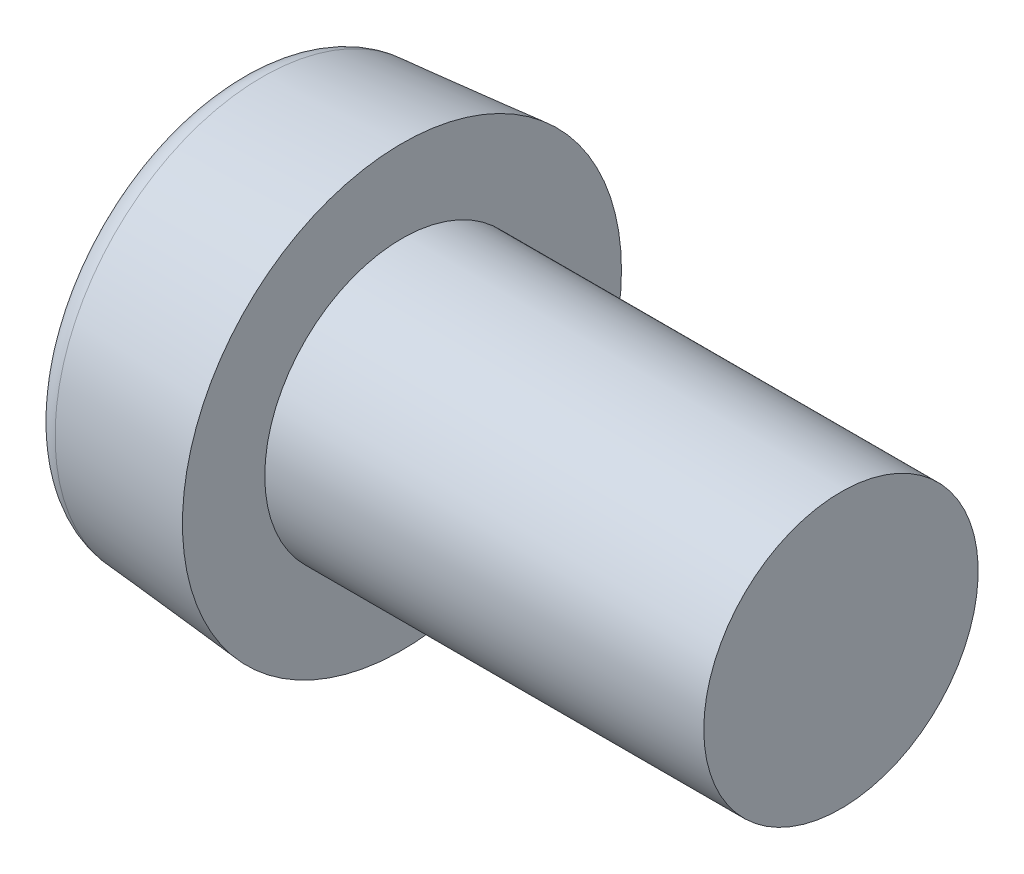
SolidWorks part; units mm, degrees
ref_plane "Front" through (0, 0, 0) normal (0, 0, 1) x (1, 0, 0)
ref_plane "Top" through (0, 0, 0) normal (0, 1, 0) x (1, 0, 0)
ref_plane "Right" through (0, 0, 0) normal (1, 0, 0) x (0, 0, -1)
ref_plane "Plane1" through (6, 0, 0) normal (1, 0, 0) x (0, 0, -1)
sketch "Sketch1" plane through (6, 0, 0) normal (1, 0, 0) x (0, 0, -1)
  circle A0 centre (0, 0) radius 8
  dimension "dk" = 16
extrude "BaseHead" add sketch "Sketch1" against normal blind 6 draft 5
sketch "Sketch2" plane through (6, 0, 0) normal (1, 0, 0) x (0, 0, -1)
  circle A0 centre (0, 0) radius 3
sketch "Sketch8" plane through (0, 0, 0) normal (0, 0, 1) x (1, 0, 0)
  line L0 (0, 0) -> (35.73, 0) construction
  line L1 (7.1525, 0) -> (7.1525, -2) construction
  line L2 (6, -8) -> (6, 8) construction
  line L3 (11.6578, 0) -> (11.6578, -9.026) construction
  line L4 (6, 5) -> (22, 5)
  line L5 (22, 5) -> (22, 0)
  line L7 (22, 0) -> (6, 0)
  line L9 (6, 5) -> (6, 0)
  arc A0 (6.7996, -0.1884) -> (7.126, -0.3991) centre (7.1525, 0) ccw construction
  dimension "r" = 0.4
  dimension "a" = 2
  dimension "d" = 10
  dimension "D4" = 9.026
  dimension "l" = 16
revolve "Revolve1" add sketch "Sketch8" angle 360 about L0
cosmetic thread "ThreadCosmetic1" [suppressed] parameters "bb"=16, "THD_MINOR"=8.376
sketch "Sketch4" plane through (0, 0, 0) normal (1, 0, 0) x (0, 0, -1)
  line L1 (0, 3.8221) -> (-3.31, 1.911) construction
  line L2 (-3.31, 1.911) -> (-3.31, -1.911) construction
  line L3 (-3.31, -1.911) -> (0, -3.8221) construction
  line L4 (0, -3.8221) -> (3.31, -1.911) construction
  line L5 (3.31, -1.911) -> (3.31, 1.911) construction
  line L6 (3.31, 1.911) -> (0, 3.8221) construction
  line L7 (1.655, 2.8665) -> (-1.655, 2.8665) construction
  line L8 (-1.655, 2.8665) -> (-3.31, 0) construction
  line L9 (-3.31, 0) -> (-1.655, -2.8665) construction
  line L10 (-1.655, -2.8665) -> (1.655, -2.8665) construction
  line L11 (1.655, -2.8665) -> (3.31, 0) construction
  line L12 (3.31, 0) -> (1.655, 2.8665) construction
  circle A0 centre (0, 0) radius 3.8221 construction
  circle A1 centre (0, 0) radius 3.31 construction
  spline S0 degree 3 poles (0, 4.4101) (1.5277, 2.646) (3.8192, 2.205) (3.0554, 0) (3.8192, -2.205) (1.5277, -2.646) (0, -4.4101) (-1.5277, -2.646) (-3.8192, -2.205) (-3.0554, 0) (-3.8192, 2.205) (-1.5277, 2.646) (0, 4.4101) (1.5277, 2.646) (3.8192, 2.205) knots -0.25 -0.166667 -0.083333 0 0.083333 0.166667 0.25 0.333333 0.416667 0.5 0.583333 0.666667 0.75 0.833333 0.916667 1 1.083333 1.166667 1.25 only from (1.655, 2.8665) to (1.655, 2.8665)
  dimension "B" = 6.62
extrude "Socket" cut sketch "Sketch4" along normal blind 3
sketch "Sketch5" plane through (3, 0, 0) normal (-1, 0, 0) x (0, 0, 1)
  spline S1 degree 3 poles (0, 4.4101) (-1.5277, 2.646) (-3.8192, 2.205) (-3.0554, 0) (-3.8192, -2.205) (-1.5277, -2.646) (0, -4.4101) (1.5277, -2.646) (3.8192, -2.205) (3.0554, 0) (3.8192, 2.205) (1.5277, 2.646) (0, 4.4101) (-1.5277, 2.646) (-3.8192, 2.205) knots -0.25 -0.166667 -0.083333 0 0.083333 0.166667 0.25 0.333333 0.416667 0.5 0.583333 0.666667 0.75 0.833333 0.916667 1 1.083333 1.166667 1.25 only from (-1.655, 2.8665) to (-1.655, 2.8665)
  spline S2 degree 3 poles (0, 4.4101) (-1.5277, 2.646) (-3.8192, 2.205) (-3.0554, 0) (-3.8192, -2.205) (-1.5277, -2.646) (0, -4.4101) (1.5277, -2.646) (3.8192, -2.205) (3.0554, 0) (3.8192, 2.205) (1.5277, 2.646) (0, 4.4101) (-1.5277, 2.646) (-3.8192, 2.205) knots -0.25 -0.166667 -0.083333 0 0.083333 0.166667 0.25 0.333333 0.416667 0.5 0.583333 0.666667 0.75 0.833333 0.916667 1 1.083333 1.166667 1.25 only from (-1.655, 2.8665) to (-1.655, 2.8665)
  dimension "D1" = 0
ref_plane "Plane2" through (4, 0, 0) normal (-1, 0, 0) x (0, 0, 1)
sketch "Sketch7" plane through (4, 0, 0) normal (-1, 0, 0) x (0, 0, 1)
  point P0 (0, 0)
loft "Cut-Loft1" cut profiles "Sketch7", "Sketch5"
sketch "Sketch6" plane through (-30.7487, 13.2487, 0) normal (0, 0, 1) x (0, -1, 0)
  line L0 (13.2487, 89.8637) -> (13.2487, 24.8312) construction
  line L1 (-5.9393, 36.7487) -> (8.9607, 36.7487)
  line L2 (-5.9393, 36.7487) -> (-5.9393, 14.7487)
  line L3 (-5.9393, 14.7487) -> (8.2487, 14.7487)
  line L4 (9.0607, 36.8487) -> (9.0607, 10.9487)
  line L5 (18.2487, 52.7487) -> (8.2487, 52.7487) construction
  line L6 (8.2487, 14.7487) -> (9.0607, 10.9487)
  line L9 (21.2487, 36.7487) -> (5.2487, 36.7487) construction
  arc A0 (8.9607, 36.7487) -> (9.0607, 36.8487) centre (8.9607, 36.8487) ccw
  dimension "d1" = 8.376
  dimension "D2" = 15
  dimension "b" = 38
  dimension "D3" = 10
  dimension "x" = 3.8
fillet "HeadFillet2" radius 1 1 edges at (0, 0, -7.4751)
sketch "Sketch9" plane through (0, 0, 0) normal (0, 0, 1) x (1, 0, 0)
  line L0 (22, 4.2968) -> (22.406, 5)
  line L1 (22.406, 5) -> (22.406, 5.812)
  line L2 (22.406, 5.812) -> (21.594, 5.812)
  line L3 (21.594, 5.812) -> (21.594, 5)
  line L4 (21.594, 5) -> (22, 4.2968)
  line L5 (22, -5) -> (22, 5) construction
  line L6 (0, 0) -> (28.2938, 0) construction
  line L7 (0, 6.5587) -> (0, -6.5587) construction
  dimension "D1" = 0.812
  dimension "D2" = 10
revolve "Cut-Revolve10" [suppressed] cut sketch "Sketch9" angle 360 about L6
pattern_linear "LPattern10" [suppressed] count 16 spacing 0.9744 along (1, 0, 0)
equation "\"D1@Plane1\"=\"k@BaseHead\""
equation "\"D1@Plane2\" = \"t@Socket\" / 3"
equation "\"D2@Sketch9\" =\"d@Sketch8\""
equation "\"D1@Sketch9\" =  ( \"d@Sketch8\" - \"THD_MINOR@ThreadCosmetic1\" )  / 2"
equation "\"D3@LPattern10\" = \"D1@Sketch9\" * 1.2"
equation "\"D1@LPattern10\" = \"bb@ThreadCosmetic1\" / \"D3@LPattern10\" "
equation "\"D3@Sketch6\" = \"d@Sketch8\""
